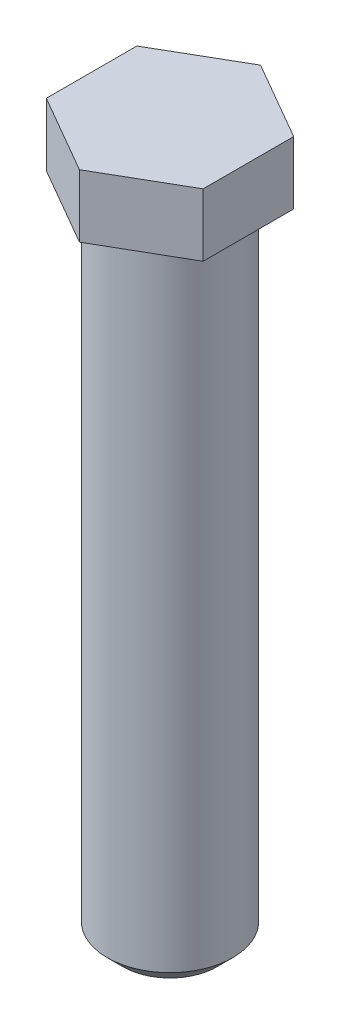
SolidWorks part; units mm, degrees
ref_plane "Front Plane" through (0, 0, 0) normal (0, 0, 1) x (1, 0, 0)
ref_plane "Top Plane" through (0, 0, 0) normal (0, 1, 0) x (1, 0, 0)
ref_plane "Right Plane" through (0, 0, 0) normal (1, 0, 0) x (0, 0, -1)
sketch "Sketch1" plane through (0, 0, 0) normal (0, 1, 0) x (1, 0, 0)
  circle A0 centre (0, 0) radius 2
  dimension "D1" = 4
extrude "Boss-Extrude1" add sketch "Sketch1" along normal blind 20.7
sketch "Sketch2" plane through (0, 20.7, 0) normal (0, 1, 0) x (1, 0, 0)
  line L1 (0, 2.8868) -> (-2.5, 1.4434)
  line L2 (-2.5, 1.4434) -> (-2.5, -1.4434)
  line L3 (-2.5, -1.4434) -> (0, -2.8868)
  line L4 (0, -2.8868) -> (2.5, -1.4434)
  line L5 (2.5, -1.4434) -> (2.5, 1.4434)
  line L6 (2.5, 1.4434) -> (0, 2.8868)
  circle A0 centre (0, 0) radius 2.5 construction
  dimension "D1" = 5
extrude "Boss-Extrude2" add sketch "Sketch2" along normal blind 2
chamfer "Chamfer1" distance 0.5 angle 45 1 edges at (0, 0, 2)
fillet "Fillet1" radius 0.2 1 edges at (0, 20.7, 2)
